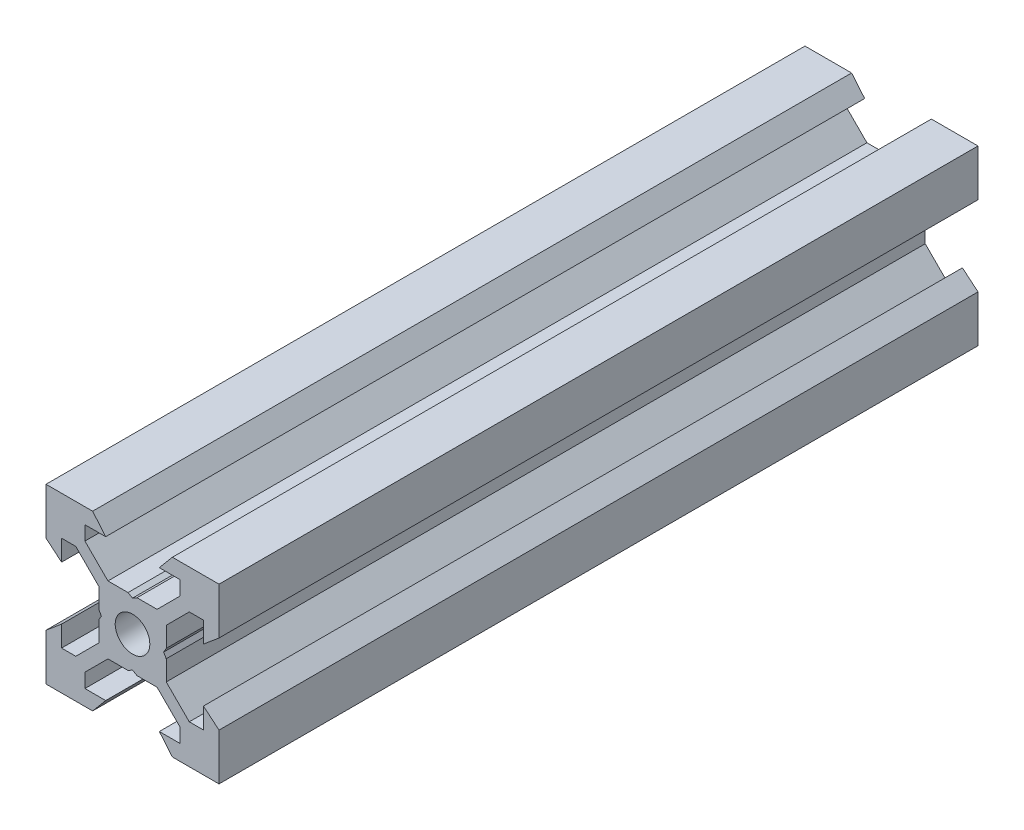
SolidWorks part; units mm, degrees
ref_plane "Front Plane" through (0, 0, 0) normal (0, 0, 1) x (1, 0, 0)
ref_plane "Top Plane" through (0, 0, 0) normal (0, 1, 0) x (1, 0, 0)
ref_plane "Right Plane" through (0, 0, 0) normal (1, 0, 0) x (0, 0, -1)
sketch "Sketch1" plane through (0, 0, 0) normal (0, 0, 1) x (1, 0, 0)
  line L0 (10, 10) -> (4.6104, 10) construction
  line L1 (10, 10) -> (10, 4.6104) construction
  line L2 (10, -10) -> (10, -4.6104) construction
  line L3 (10, -10) -> (4.6104, -10) construction
  line L4 (10, 10) -> (10, 4.6104)
  line L5 (6.5607, 5.5) -> (8.2, 5.5)
  line L6 (5.5, 8.2) -> (5.5, 6.5607)
  line L7 (10, 10) -> (4.6104, 10)
  line L8 (10, 10) -> (10, 4.6104)
  line L9 (6.5607, 5.5) -> (3.9, 2.8393)
  line L10 (5.5, 6.5607) -> (2.8393, 3.9)
  line L11 (10, 4.6104) -> (8.2, 3.1)
  line L12 (4.6104, 10) -> (3.1, 8.2)
  line L13 (8.2, 3.1) -> (8.2, 5.5)
  line L14 (3.1, 8.2) -> (5.5, 8.2)
  line L15 (-6.5607, 5.5) -> (-8.2, 5.5)
  line L16 (6.5607, -5.5) -> (8.2, -5.5)
  line L17 (3.1, -8.2) -> (5.5, -8.2)
  line L18 (8.2, -3.1) -> (8.2, -5.5)
  line L19 (4.6104, -10) -> (3.1, -8.2)
  line L20 (10, -4.6104) -> (8.2, -3.1)
  line L21 (0.5196, -3.9) -> (0, -3.6)
  line L22 (0.5196, 3.9) -> (0, 3.6)
  line L23 (3.6, 0) -> (3.9, -0.5196)
  line L24 (3.9, 0.5196) -> (3.6, 0)
  line L25 (3.9, 0.5196) -> (3.9, 2.8393)
  line L26 (2.8393, 3.9) -> (0.5196, 3.9)
  line L27 (3.9, -2.8393) -> (3.9, -0.5196)
  line L28 (2.8393, -3.9) -> (0.5196, -3.9)
  line L29 (5.5, -6.5607) -> (2.8393, -3.9)
  line L30 (6.5607, -5.5) -> (3.9, -2.8393)
  line L31 (10, -10) -> (10, -4.6104)
  line L32 (10, -10) -> (4.6104, -10)
  line L33 (5.5, -8.2) -> (5.5, -6.5607)
  line L34 (-6.5607, -5.5) -> (-8.2, -5.5)
  line L35 (10, -10) -> (10, -4.6104)
  line L36 (0, 0) -> (0, 8.2) construction
  line L37 (-10, -10) -> (-4.6104, -10) construction
  line L38 (-10, -10) -> (-10, -4.6104) construction
  line L39 (-10, 10) -> (-10, 4.6104) construction
  line L40 (-10, 10) -> (-4.6104, 10) construction
  line L41 (-10, -10) -> (-10, -4.6104)
  line L43 (-5.5, -8.2) -> (-5.5, -6.5607)
  line L44 (-10, -10) -> (-4.6104, -10)
  line L45 (-10, -10) -> (-10, -4.6104)
  line L46 (-6.5607, -5.5) -> (-3.9, -2.8393)
  line L47 (-5.5, -6.5607) -> (-2.8393, -3.9)
  line L48 (-2.8393, -3.9) -> (-0.5196, -3.9)
  line L49 (-3.9, -2.8393) -> (-3.9, -0.5196)
  line L50 (-2.8393, 3.9) -> (-0.5196, 3.9)
  line L51 (-3.9, 0.5196) -> (-3.9, 2.8393)
  line L52 (-3.9, 0.5196) -> (-3.6, 0)
  line L53 (-3.6, 0) -> (-3.9, -0.5196)
  line L54 (-0.5196, 3.9) -> (0, 3.6)
  line L55 (-0.5196, -3.9) -> (0, -3.6)
  line L56 (-10, -4.6104) -> (-8.2, -3.1)
  line L57 (-4.6104, -10) -> (-3.1, -8.2)
  line L58 (-8.2, -3.1) -> (-8.2, -5.5)
  line L59 (-3.1, -8.2) -> (-5.5, -8.2)
  line L60 (-10, -10) -> (10, -10) construction
  line L61 (-10, -10) -> (-10, 10) construction
  line L62 (-3.1, 8.2) -> (-5.5, 8.2)
  line L63 (-8.2, 3.1) -> (-8.2, 5.5)
  line L64 (-4.6104, 10) -> (-3.1, 8.2)
  line L65 (-10, 4.6104) -> (-8.2, 3.1)
  line L66 (-5.5, 6.5607) -> (-2.8393, 3.9)
  line L67 (-6.5607, 5.5) -> (-3.9, 2.8393)
  line L68 (-10, 10) -> (-10, 4.6104)
  line L69 (-10, 10) -> (-4.6104, 10)
  line L70 (-5.5, 8.2) -> (-5.5, 6.5607)
  line L71 (-10, 10) -> (10, 10) construction
  line L72 (-10, 10) -> (-10, 4.6104)
  line L73 (10, -10) -> (10, 10) construction
  line L74 (-10, -10) -> (10, 10) construction
  line L75 (-10, 10) -> (10, -10) construction
  circle A0 centre (0, 0) radius 2
  dimension "D7" = 4
  dimension "D1" = 20
  dimension "D2" = 5.3896
  dimension "D3" = 4.5
  dimension "D4" = 50
  dimension "D5" = 1.8
  dimension "D6" = 1.5104
  dimension "D8" = 5.5
  dimension "D9" = 120
  dimension "D10" = 0.3
  dimension "D11" = 2.3197
  dimension "D12" = 7.8
  dimension "D13" = 7.8
  dimension "D14" = 1.5
  dimension "D15" = 2.6607
extrude "Boss-Extrude1" add sketch "Sketch1" along normal mid plane 87.73 contours L70 L62 L64 L69 L68 L65 L63 L15 L67 L51 L52 L53 L49 L46 L34 L58 L56 L41 L44 L57 L59 L43 L47 L48 L55 L21 L28 L29 L33 L17 L19 L32 L31 L20 L18 L16 L30 L27 L23 L24 L25 L9 L5 L13 L11 L4 L7 L12 L14 L6 L10
